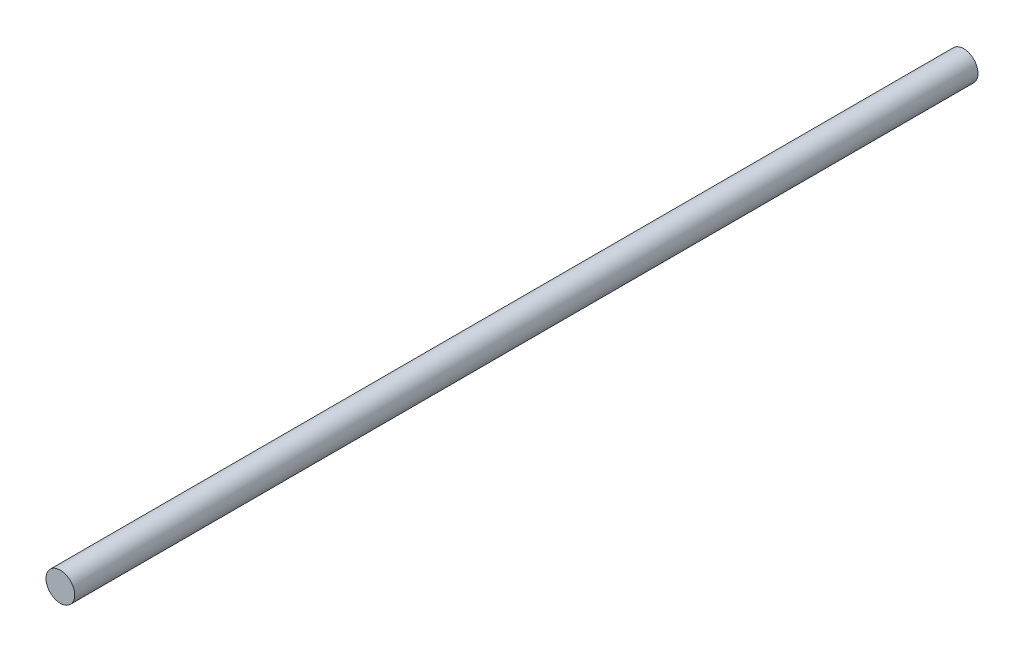
SolidWorks part; units mm, degrees
ref_plane "前视基准面" through (0, 0, 0) normal (0, 0, 1) x (1, 0, 0)
ref_plane "上视基准面" through (0, 0, 0) normal (0, 1, 0) x (1, 0, 0)
ref_plane "右视基准面" through (0, 0, 0) normal (1, 0, 0) x (0, 0, -1)
sketch "草图1" plane through (0, 0, 0) normal (0, 0, 1) x (1, 0, 0)
  circle A0 centre (0, 0) radius 4
extrude "凸台-拉伸1" add sketch "草图1" along normal blind 251.5
